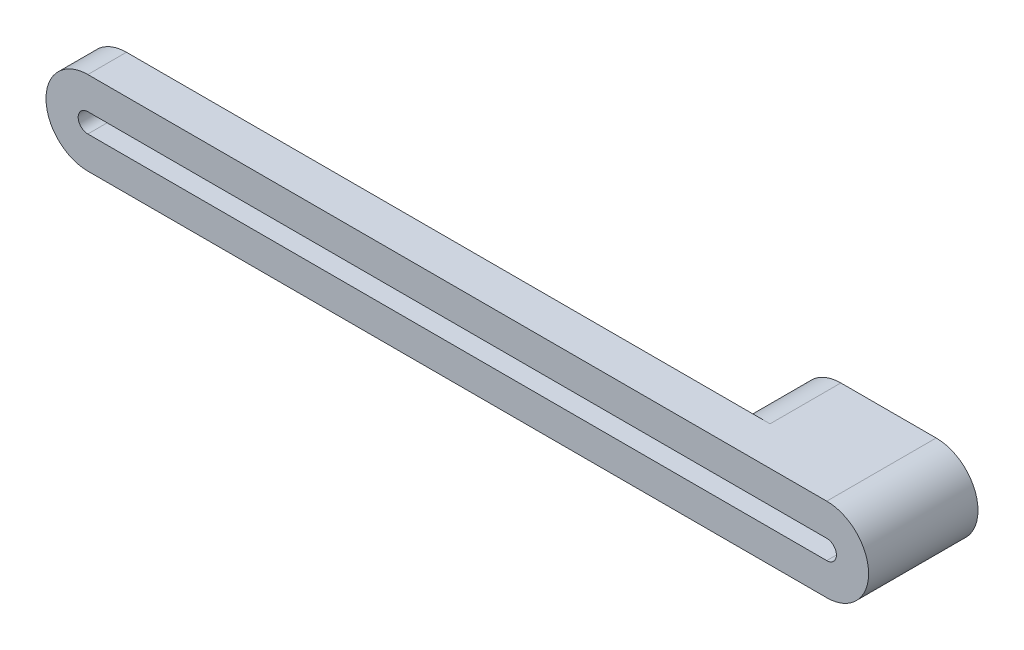
SolidWorks part; units mm, degrees
ref_plane "Front Plane" through (0, 0, 0) normal (0, 0, 1) x (1, 0, 0)
ref_plane "Top Plane" through (0, 0, 0) normal (0, 1, 0) x (1, 0, 0)
ref_plane "Right Plane" through (0, 0, 0) normal (1, 0, 0) x (0, 0, -1)
sketch "Sketch1" plane through (0, 0, 0) normal (0, 0, 1) x (1, 0, 0)
  line L4 (-68.8658, 22.7918) -> (-83.6757, 22.7918)
  line L5 (-68.8658, 9.7918) -> (-83.6757, 9.7918)
  line L6 (-68.8658, 17.7918) -> (-83.6757, 17.7918)
  line L7 (-68.8658, 14.7918) -> (-83.6757, 14.7918)
  arc A7 (-83.6757, 22.7918) -> (-83.6757, 9.7918) centre (-83.6757, 16.2918) ccw
  arc A8 (-68.8658, 22.7918) -> (-68.8658, 9.7918) centre (-68.8658, 16.2918) cw
  arc A9 (-83.6757, 17.7918) -> (-83.6757, 14.7918) centre (-83.6757, 16.2918) ccw
  arc A10 (-68.8658, 17.7918) -> (-68.8658, 14.7918) centre (-68.8658, 16.2918) cw
  dimension "D1" = 5
extrude "Boss-Extrude1" add sketch "Sketch1" along normal blind 11
sketch "Sketch2" plane through (0, 0, 11) normal (0, 0, 1) x (1, 0, 0)
  line L10 (-183.6757, 22.7918) -> (-83.6757, 22.7918)
  line L11 (-83.6757, 22.7918) -> (-68.8658, 22.7918)
  line L12 (-83.6757, 9.7918) -> (-68.8658, 9.7918)
  line L13 (-183.6757, 9.7918) -> (-83.6757, 9.7918)
  line L14 (-183.6757, 17.7918) -> (-83.6757, 17.7918)
  line L15 (-83.6757, 17.7918) -> (-68.8658, 17.7918)
  line L16 (-83.6757, 14.7918) -> (-68.8658, 14.7918)
  line L17 (-183.6757, 14.7918) -> (-83.6757, 14.7918)
  arc A2 (-68.8658, 22.7918) -> (-68.8658, 9.7918) centre (-68.8658, 16.2918) cw
  arc A6 (-183.6757, 22.7918) -> (-183.6757, 9.7918) centre (-183.6757, 16.2918) ccw
  arc A8 (-68.8658, 17.7918) -> (-68.8658, 14.7918) centre (-68.8658, 16.2918) cw
  arc A9 (-183.6757, 17.7918) -> (-183.6757, 14.7918) centre (-183.6757, 16.2918) ccw
  dimension "D1" = 5
extrude "Boss-Extrude2" add sketch "Sketch2" along normal blind 6
